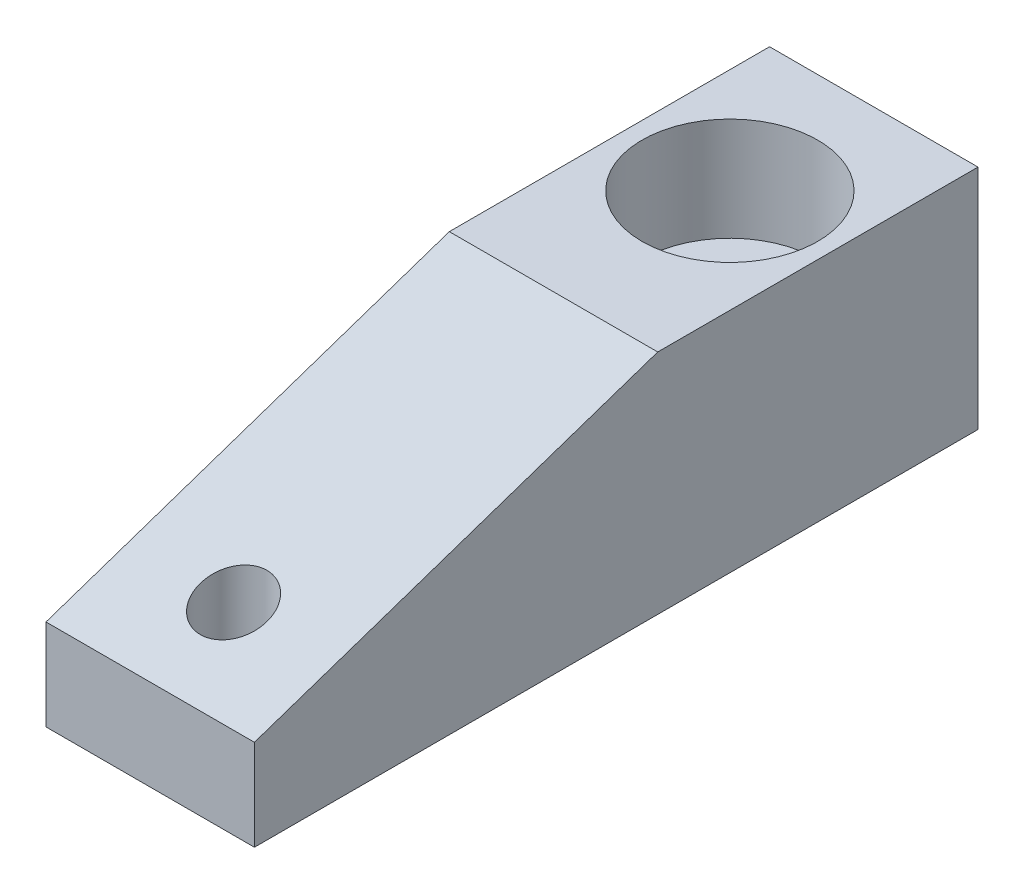
SolidWorks part; units mm, degrees
material "Alloy Steel"
ref_plane "Front Plane" through (0, 0, 0) normal (0, 0, 1) x (1, 0, 0)
ref_plane "Top Plane" through (0, 0, 0) normal (0, 1, 0) x (1, 0, 0)
ref_plane "Right Plane" through (0, 0, 0) normal (1, 0, 0) x (0, 0, -1)
sketch "Sketch1" plane through (0, 0, 0) normal (0, 1, 0) x (1, 0, 0)
  line L1 (0, 0) -> (16.002, 0)
  line L2 (0, 0) -> (0, -55.5498)
  line L3 (0, -55.5498) -> (16.002, -55.5498)
  line L4 (16.002, 0) -> (16.002, -55.5498)
  dimension "D1" = 16.002
  dimension "D2" = 55.5498
extrude "Extrude1" add sketch "Sketch1" along normal blind 17.4498
ref_plane "Plane1" through (8.0518, 0, 0) normal (1, 0, 0) x (0, 0, -1)
sketch "Sketch3" plane through (8.0518, 0, 0) normal (1, 0, 0) x (0, 0, -1)
  line L0 (-11.0998, 31.6794) -> (-11.0998, -3.5955) construction
  line L1 (0, 17.4498) -> (0, 0) construction
  line L2 (-17.8435, 17.4498) -> (-17.8435, 9.525)
  line L3 (-55.5498, 17.4498) -> (0, 17.4498) construction
  line L4 (-17.8435, 9.525) -> (-15.4686, 9.525)
  line L5 (-15.4686, 9.525) -> (-15.4686, 6.6548)
  line L6 (-15.4686, 6.6548) -> (-16.9412, 6.6548)
  line L7 (-16.9412, 6.6548) -> (-17.3482, 0)
  line L8 (-55.5498, 0) -> (0, 0) construction
  line L9 (-17.3482, 0) -> (-11.0998, 0)
  line L10 (-11.0998, 0) -> (-11.0998, 17.4498)
  line L11 (-11.0998, 17.4498) -> (-17.8435, 17.4498)
  dimension "D1" = 11.0998
  dimension "D2" = 13.4874
  dimension "D3" = 7.9248
  dimension "D4" = 8.7376
  dimension "D5" = 6.6548
  dimension "D6" = 3.5
  dimension "D7" = 12.4968
revolve "Cut-Revolve1" cut sketch "Sketch3" angle 360 about L0
fillet "Fillet1" radius 0.381 1 edges at (8.0518, 6.6548, 16.9412)
sketch "Sketch4" plane through (16.002, 0, 0) normal (1, 0, 0) x (0, 0, -1)
  line L0 (-55.5498, 6.9799) -> (-55.5498, 17.4498)
  line L1 (-55.5498, 17.4498) -> (0, 17.4498) construction
  line L2 (-55.5498, 17.4498) -> (-24.5872, 17.4498)
  line L3 (-55.5498, 6.9799) -> (-24.5872, 17.4498)
  line L4 (-55.5498, 17.4498) -> (-55.5498, 0) construction
  line L6 (-11.0998, 9.525) -> (-11.0998, 17.4498) construction
  line L7 (-55.5498, 0) -> (0, 0) construction
  dimension "D1" = 13.4874
  dimension "D2" = 6.9799
extrude "Cut-Extrude1" cut sketch "Sketch4" against normal through all
sketch "Sketch5" plane through (0, 0, 0) normal (0, -1, 0) x (1, 0, 0)
  circle A0 centre (8.0518, 49.1998) radius 2.5527
  dimension "D1" = 5.1054
  dimension "D2" = 38.1
extrude "Cut-Extrude2" cut sketch "Sketch5" against normal through all
